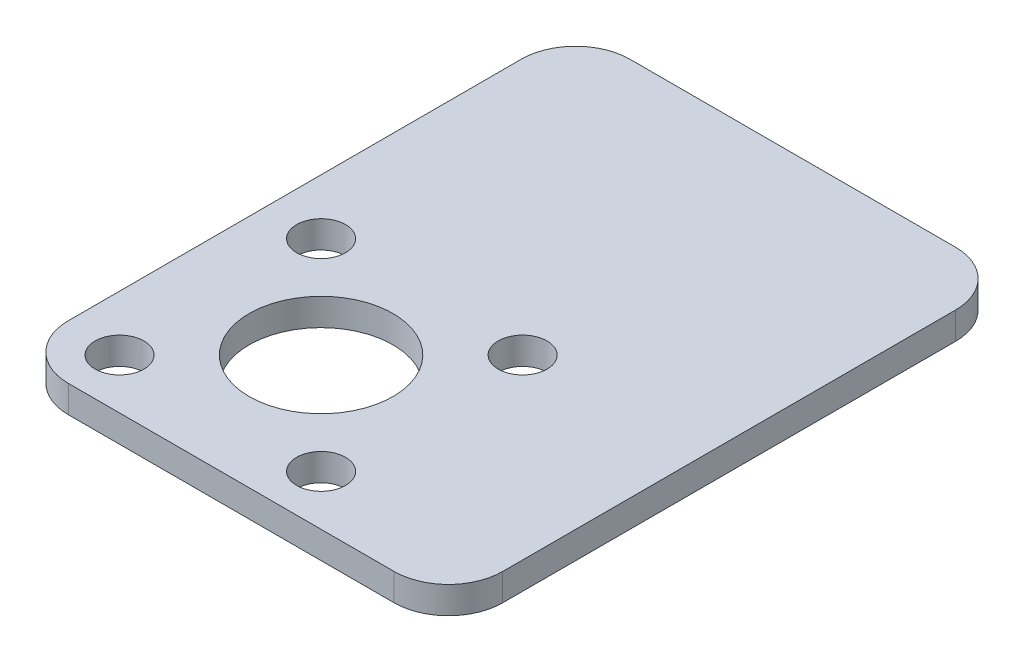
SolidWorks part; units mm, degrees
ref_plane "Alzado" through (0, 0, 0) normal (0, 0, 1) x (1, 0, 0)
ref_plane "Planta" through (0, 0, 0) normal (0, 1, 0) x (1, 0, 0)
ref_plane "Vista lateral" through (0, 0, 0) normal (1, 0, 0) x (0, 0, -1)
sketch "Croquis1" plane through (0, 0, 0) normal (0, 1, 0) x (1, 0, 0)
  line L0 (-16, -9.565) -> (16, -9.565) construction
  line L1 (-16, 20.685) -> (16, 20.685)
  line L2 (-16, 20.685) -> (-16, -20.685)
  line L3 (-16, -20.685) -> (16, -20.685)
  line L4 (16, 20.685) -> (16, -20.685)
  line L5 (-16, 20.685) -> (16, -20.685) construction
  line L6 (-16, -20.685) -> (16, 20.685) construction
  line L7 (-4.5, -20.685) -> (-4.5, 20.685) construction
  circle A0 centre (-4.5, -9.565) radius 5.3
  point P0 (0, 0)
  dimension "D3" = 10.6
  dimension "D1" = 41.37
  dimension "D2" = 32
  dimension "D4" = 11.12
  dimension "D5" = 11.5
extrude "Saliente-Extruir1" add sketch "Croquis1" along normal blind 2
sketch "Croquis2" plane through (0, 2, 0) normal (0, 1, 0) x (1, 0, 0)
  line L0 (-4.5, -9.565) -> (2.9246, -16.9896) construction
  line L1 (-4.5, -9.565) -> (6, -9.565) construction
  circle A0 centre (-4.5, -9.565) radius 10.5 construction
  circle A1 centre (-4.5, -9.565) radius 5.3 construction
  circle A2 centre (2.9246, -16.9896) radius 1.8
  dimension "D1" = 21
  dimension "D2" = 3.6
  dimension "D3" = 45
extrude "Cortar-Extruir1" cut sketch "Croquis2" against normal up to next (2 mm away)
pattern_circular "MatrizC1" count 4 over 360 about axis through (-4.5, 0, 9.565) along (0, 1, 0) of "Cortar-Extruir1"
fillet "Redondeo1" radius 4 4 edges at (-16, 1, -20.685) (16, 1, -20.685) (16, 1, 20.685) (-16, 1, 20.685)
